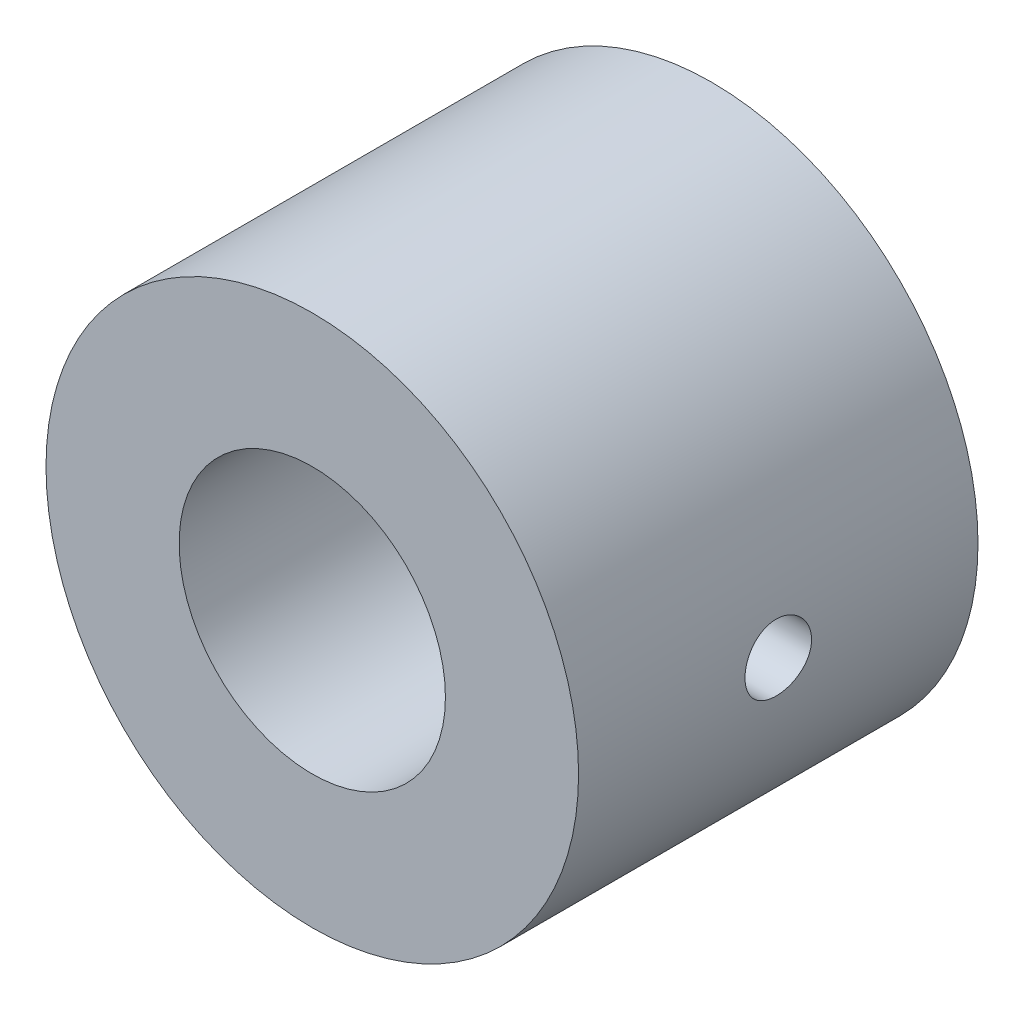
SolidWorks part; units mm, degrees
ref_plane "Plan de face" through (0, 0, 0) normal (0, 0, 1) x (1, 0, 0)
ref_plane "Plan de dessus" through (0, 0, 0) normal (0, 1, 0) x (1, 0, 0)
ref_plane "Plan de droite" through (0, 0, 0) normal (1, 0, 0) x (0, 0, -1)
sketch "Esquisse1" plane through (0, 0, 0) normal (0, 0, 1) x (1, 0, 0)
  circle A0 centre (0, 0) radius 5
  circle A1 centre (0, 0) radius 10
extrude "Boss.-Extru.1" add sketch "Esquisse1" along normal blind 15
sketch "Esquisse2" plane through (0, 0, 0) normal (1, 0, 0) x (0, 0, -1)
  line L0 (0, 0) -> (-15, 0) construction
  line L1 (-15, 10) -> (-15, -10) construction
  line L2 (-7.5, 8.0881) -> (-7.5, -7.4925) construction
ref_plane "Plan1" through (10, 0, 0) normal (1, 0, 0) x (0, 0, -1)
ref_plane "Plan2" through (-10, 0, 0) normal (1, 0, 0) x (0, 0, -1)
hole_wizard "Trou taraudé M31" positions "Esquisse5" profile "Esquisse6" tap size "M3" standard "DIN"
sketch "Esquisse5" plane through (10, 0, 0) normal (1, 0, 0) x (0, 0, -1)
  line L0 (0, 0) -> (-15, 0) construction
  point P0 (-7.5, 0)
sketch "Esquisse6" plane through (10, 0, 7.5) normal (0, 1, 0) x (0, 0, -1)
  line L0 (0, 0) -> (0, 9.2511)
  line L1 (0, 9.2511) -> (1.25, 8.5)
  line L2 (1.25, 8.5) -> (1.25, 0)
  line L5 (1.25, 0) -> (0, 0)
  line L10 (0, 9.2511) -> (-1.25, 8.5) construction
  line L11 (0, -6.35) -> (0, 107.95) construction
  dimension "Diamètre du trou pour taraudage" = 2.5
  dimension "Profondeur du trou pour taraudage" = 8.5
  dimension "Angle de pointe" = 118
cosmetic thread "Filetage de perçage1" parameters "D1"=5.1588, "D2"=3
hole_wizard "Trou taraudé M32" positions "Esquisse7" profile "Esquisse8" tap size "M3" standard "DIN"
sketch "Esquisse7" plane through (-10, 0, 0) normal (1, 0, 0) x (0, 0, -1)
  line L0 (0, 0) -> (-15, 0) construction
  point P0 (-7.5, 0)
sketch "Esquisse8" plane through (-10, 0, 7.5) normal (0, 1, 0) x (0, 0, 1)
  line L0 (0, 0) -> (0, 9.2511)
  line L1 (0, 9.2511) -> (1.25, 8.5)
  line L2 (1.25, 8.5) -> (1.25, 0)
  line L5 (1.25, 0) -> (0, 0)
  line L10 (0, 9.2511) -> (-1.25, 8.5) construction
  line L11 (0, -6.35) -> (0, 107.95) construction
  dimension "Diamètre du trou pour taraudage" = 2.5
  dimension "Profondeur du trou pour taraudage" = 8.5
  dimension "Angle de pointe" = 118
cosmetic thread "Filetage de perçage2" parameters "D1"=5.1588, "D2"=3
